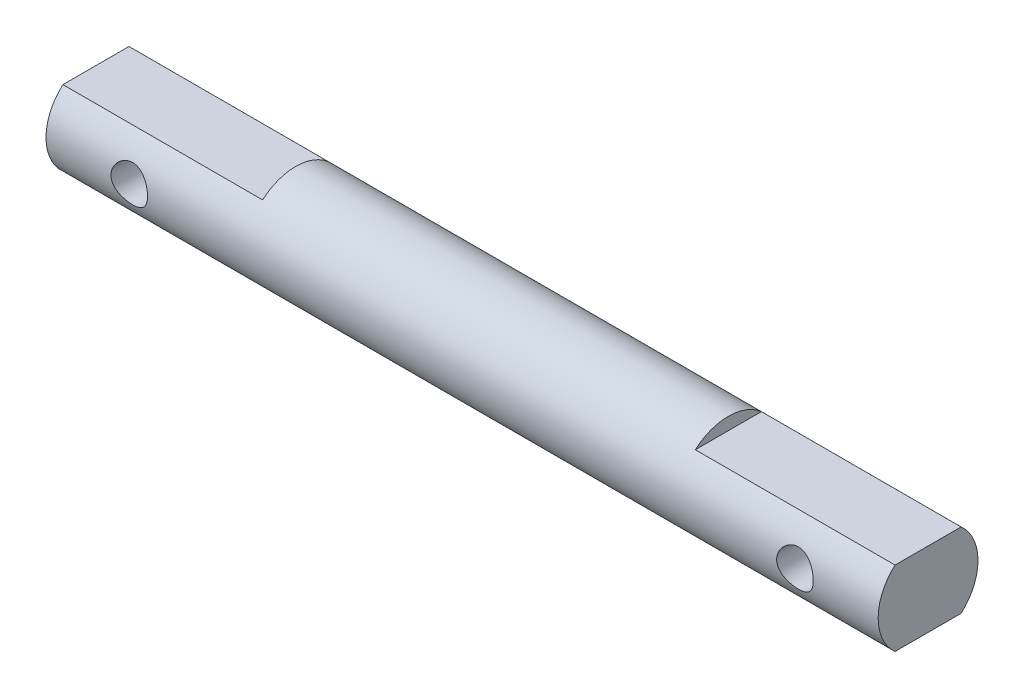
SolidWorks part; units mm, degrees
material "Plain Carbon Steel"
ref_plane "Front Plane" through (0, 0, 0) normal (0, 0, 1) x (1, 0, 0)
ref_plane "Top Plane" through (0, 0, 0) normal (0, 1, 0) x (1, 0, 0)
ref_plane "Right Plane" through (0, 0, 0) normal (1, 0, 0) x (0, 0, -1)
sketch "Sketch1" plane through (0, 0, 0) normal (0, 0, 1) x (1, 0, 0)
  line L0 (0, 0) -> (45.9529, 0) construction
  line L1 (-25, 3) -> (25, 3)
  line L2 (-25, 3) -> (-25, 0)
  line L3 (-25, 0) -> (25, 0)
  line L4 (25, 3) -> (25, 0)
  line L5 (0, 0) -> (0, 22.8572) construction
  dimension "D1" = 6
  dimension "D2" = 50
revolve "Revolve1" add sketch "Sketch1" angle 360 about L0
sketch "Sketch2" plane through (0, 0, 0) normal (0, 0, 1) x (1, 0, 0)
  line L0 (0, 0) -> (-31.5706, 0) construction
  line L1 (-25, 3) -> (-13, 3)
  line L2 (-25, 3) -> (-25, 2.25)
  line L3 (-25, 2.25) -> (-13, 2.25)
  line L4 (-13, 3) -> (-13, 2.25)
  line L5 (-25, -2.25) -> (-13, -2.25)
  line L6 (-25, -2.25) -> (-25, -3)
  line L7 (-25, -3) -> (-13, -3)
  line L8 (-13, -2.25) -> (-13, -3)
  line L9 (13, 3) -> (25, 3)
  line L10 (13, 3) -> (13, 2.25)
  line L11 (13, 2.25) -> (25, 2.25)
  line L12 (25, 3) -> (25, 2.25)
  line L13 (25, -2.25) -> (13, -2.25)
  line L14 (25, -2.25) -> (25, -3)
  line L15 (25, -3) -> (13, -3)
  line L16 (13, -2.25) -> (13, -3)
  line L17 (-25, 3) -> (-25, -3) construction
  line L18 (25, -3) -> (25, 3) construction
  line L19 (25, 3) -> (-25, 3) construction
  line L20 (-25, -3) -> (25, -3) construction
  dimension "D1" = 4.5
  dimension "D2" = 12
extrude "Cut-Extrude1" cut sketch "Sketch2" against normal through all and the other way through all
sketch "Sketch3" plane through (0, 0, 0) normal (0, 0, 1) x (1, 0, 0)
  line L0 (20, 0) -> (25, 0) construction
  line L1 (25, -2.25) -> (25, 2.25) construction
  line L2 (-20, 0) -> (-25, 0) construction
  line L3 (-25, 2.25) -> (-25, -2.25) construction
  circle A0 centre (-20, 0) radius 1.1
  circle A1 centre (20, 0) radius 1.1
  dimension "D1" = 2.2
  dimension "D2" = 5
extrude "Cut-Extrude2" cut sketch "Sketch3" against normal through all and the other way through all
